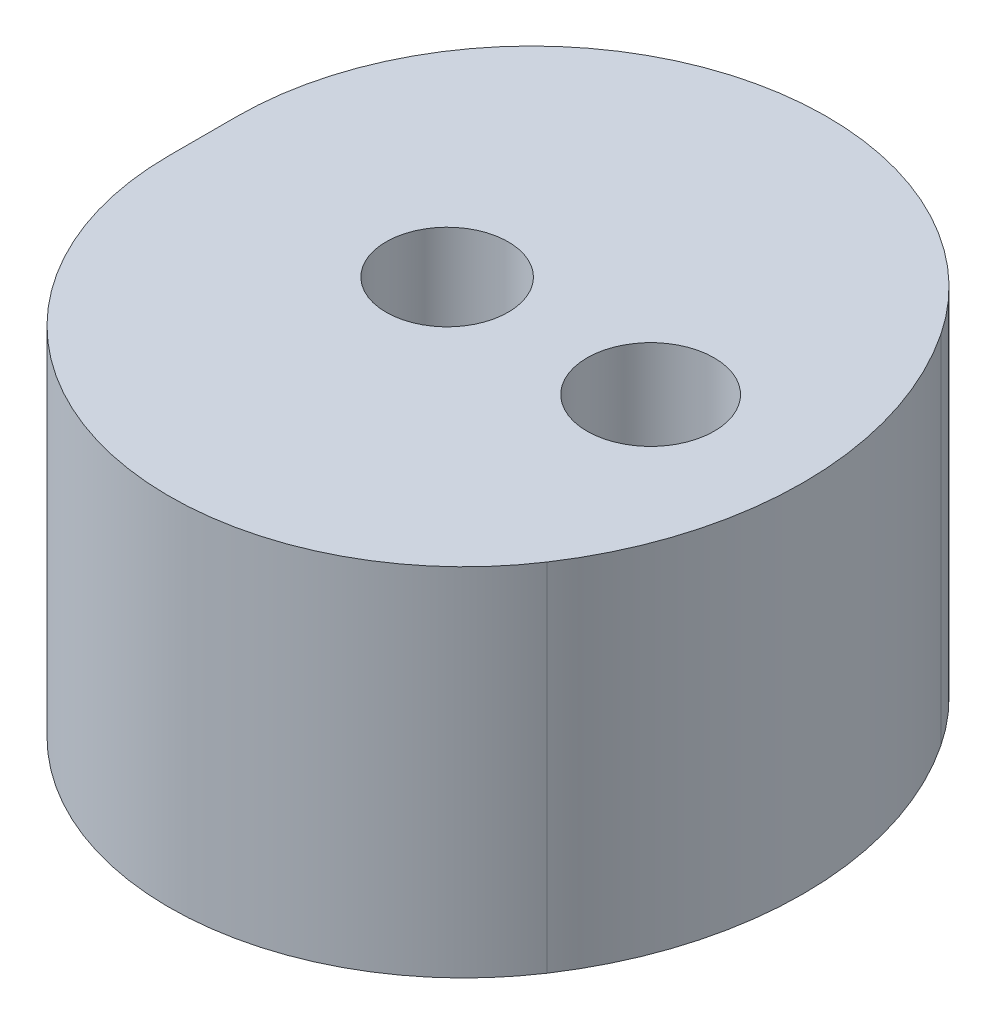
SolidWorks part; units mm, degrees
ref_plane "Front Plane" through (0, 0, 0) normal (0, 0, 1) x (1, 0, 0)
ref_plane "Top Plane" through (0, 0, 0) normal (0, 1, 0) x (1, 0, 0)
ref_plane "Right Plane" through (0, 0, 0) normal (1, 0, 0) x (0, 0, -1)
sketch "Sketch1" plane through (0, 0, 0) normal (0, 1, 0) x (1, 0, 0)
  line L0 (0, 0) -> (0, 28.2467) construction
  line L1 (28.5, 0) -> (28.5, 28.2467) construction
  line L2 (0, 28.2467) -> (28.5, 28.2467) construction
  line L3 (7, 28.2467) -> (7, 0) construction
  line L4 (21.5, 28.2467) -> (21.5, 0) construction
  line L5 (14.25, 28.2467) -> (14.25, 0) construction
  line L6 (9.45, 19.2184) -> (9.45, 9.0282)
  circle A0 centre (14.25, 14.1233) radius 7 construction
  circle A1 centre (14.25, 14.1233) radius 1.2
  circle A2 centre (18.25, 14.1233) radius 1.25
  arc A3 (9.45, 19.2184) -> (9.45, 9.0282) centre (14.25, 14.1233) cw
  dimension "D4" = 14
  dimension "D7" = 2.4
  dimension "D8" = 2.5
  dimension "D1" = 28.5
  dimension "D2" = 14.5
  dimension "D3" = 7
  dimension "D5" = 4
  dimension "D6" = 4.8
extrude "Boss-Extrude1" add sketch "Sketch1" along normal blind 7
sketch "Sketch2" plane through (0, 7, 0) normal (0, 1, 0) x (1, 0, 0)
  circle A0 centre (14.25, 14.1233) radius 2.15
  circle A1 centre (18.25, 14.1233) radius 2.15 construction
  dimension "D1" = 4.3
extrude "Cut-Extrude1" [suppressed] cut sketch "Sketch2" against normal blind 2.2
sketch "Sketch3" plane through (0, 0, 0) normal (0, -1, 0) x (1, 0, 0)
  circle A0 centre (14.25, -14.1233) radius 2.15 construction
  circle A1 centre (18.25, -14.1233) radius 2.15 construction
  circle A2 centre (14.25, -14.1233) radius 2.15 construction
  circle A3 centre (18.25, -14.1233) radius 2.15
  circle M5 centre (18.25, -14.1233) radius 1.25
extrude "Cut-Extrude3" cut sketch "Sketch3" against normal blind 3.5 contours A3 M5 | A2
sketch "Sketch4" [suppressed] plane through (0, 0, 0) normal (0, -1, 0) x (1, 0, 0)
  circle A0 centre (14.25, -14.1233) radius 2.15 construction
  circle A1 centre (14.25, -14.1233) radius 2.15
extrude "Cut-Extrude4" [suppressed] cut sketch "Sketch4" against normal blind 2.2
sketch "Sketch5" [suppressed] plane through (0, 7, 0) normal (0, 1, 0) x (1, 0, 0)
  circle A0 centre (18.25, 14.1233) radius 2.15 construction
  circle A1 centre (18.25, 14.1233) radius 2.15
extrude "Cut-Extrude5" [suppressed] cut sketch "Sketch5" against normal blind 3.5
fillet "Fillet1" radius 5.8 2 edges at (9.45, 3.5, -19.2184) (9.45, 3.5, -9.0282)
